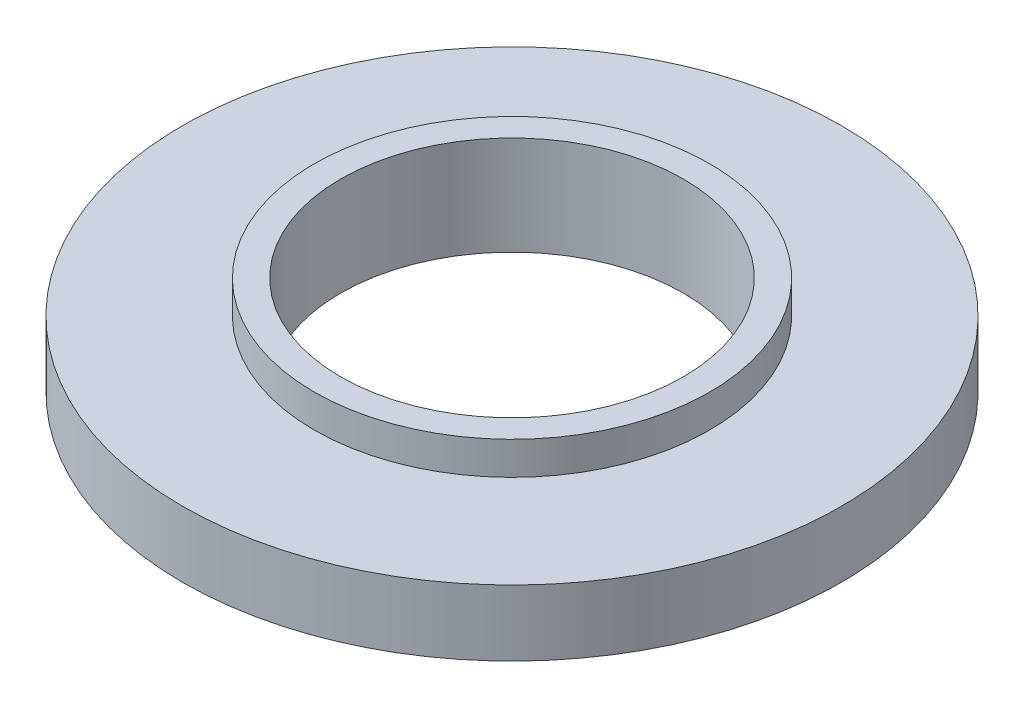
SolidWorks part; units mm, degrees
material "Plain Carbon Steel"
ref_plane "Front Plane" through (0, 0, 0) normal (0, 0, 1) x (1, 0, 0)
ref_plane "Top Plane" through (0, 0, 0) normal (0, 1, 0) x (1, 0, 0)
ref_plane "Right Plane" through (0, 0, 0) normal (1, 0, 0) x (0, 0, -1)
sketch "Sketch2" plane through (0, 0, 0) normal (0, 0, 1) x (1, 0, 0)
  line L0 (0, 8.661) -> (0, -8.0627) construction
  line L2 (2.6, 0) -> (2.6, 1.5)
  line L3 (2.6, 1.5) -> (3, 1.5)
  line L4 (3, 1.5) -> (3, 1)
  line L5 (3, 1) -> (5, 1)
  line L6 (5, 1) -> (5, 0)
  line L9 (5, 0) -> (2.6, 0)
  point P3 (2, 0.0522)
  dimension "D1" = 10
  dimension "D2" = 0.4
  dimension "D3" = 1
  dimension "D4" = 0.5
  dimension "D5" = 2
revolve "Revolve1" add sketch "Sketch2" angle 360 about L0
